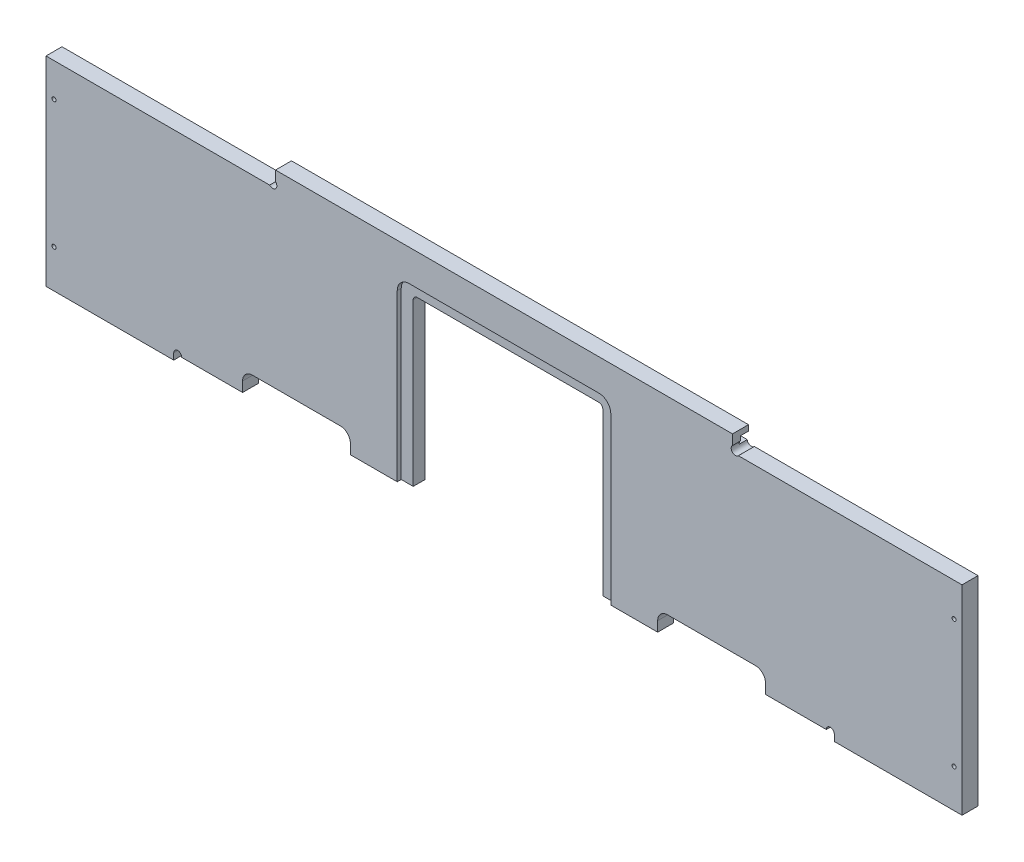
SolidWorks part; units mm, degrees
material "Pine"
ref_plane "Front Plane" through (0, 0, 0) normal (0, 0, 1) x (1, 0, 0)
ref_plane "Top Plane" through (0, 0, 0) normal (0, 1, 0) x (1, 0, 0)
ref_plane "Right Plane" through (0, 0, 0) normal (1, 0, 0) x (0, 0, -1)
sketch "Sketch1" plane through (0, 0, 0) normal (0, 0, 1) x (1, 0, 0)
  line L0 (-5300.6625, 1520.825) -> (-5451.475, 1520.825)
  line L1 (-5456.2375, 1384.3) -> (-5456.2375, 1516.0625)
  line L2 (-5557.8375, 1546.225) -> (-5194.3, 1546.225)
  line L3 (-5557.8375, 1539.875) -> (-5194.3, 1539.875)
  line L4 (-5297.4875, 1377.95) -> (-5454.65, 1377.95)
  line L5 (-5291.1375, 1384.3) -> (-5291.1375, 1516.0625)
  line L6 (-5300.6625, 1525.5875) -> (-5451.475, 1525.5875)
  line L7 (-5461, 1384.3) -> (-5461, 1516.0625)
  line L8 (-5297.4875, 1382.7125) -> (-5454.65, 1382.7125)
  line L9 (-5295.9, 1384.3) -> (-5295.9, 1516.0625)
  line L10 (-5740.4, 998.5375) -> (-5740.4, 1181.1)
  line L11 (-5740.4, 1181.1) -> (-5512.5938, 1181.1)
  line L12 (-5512.5938, 1181.1) -> (-5512.5938, 998.5375)
  line L13 (-5512.5938, 998.5375) -> (-5740.4, 998.5375)
  line L14 (-5258.5938, 1181.1) -> (-5486.4, 1181.1)
  line L15 (-5258.5938, 998.5375) -> (-5258.5938, 1181.1)
  line L16 (-5486.4, 998.5375) -> (-5258.5938, 998.5375)
  line L17 (-5486.4, 1181.1) -> (-5486.4, 998.5375)
  line L18 (-5740.4, 898.525) -> (-5011.7375, 898.525)
  line L19 (-5168.1062, 1384.3) -> (-5168.1062, 1392.2375)
  line L20 (-5176.0437, 1400.175) -> (-5245.8937, 1400.175)
  line L21 (-5253.8313, 1392.2375) -> (-5253.8313, 1384.3)
  line L22 (-5451.475, 1512.8875) -> (-5451.475, 1384.3)
  line L23 (-5303.8375, 1516.0625) -> (-5448.3, 1516.0625)
  line L24 (-5498.3062, 1384.3) -> (-5451.475, 1384.3)
  line L25 (-5253.8313, 1384.3) -> (-5300.6625, 1384.3)
  line L26 (-5584.0312, 1384.3) -> (-5740.4, 1384.3)
  line L27 (-5564.1875, 1536.7) -> (-5740.4, 1536.7)
  line L28 (-5740.4, 1357.3125) -> (-5740.4, 1206.5)
  line L29 (-5011.7375, 1357.3125) -> (-5740.4, 1357.3125)
  line L30 (-5011.7375, 1206.5) -> (-5011.7375, 1357.3125)
  line L31 (-5740.4, 1206.5) -> (-5011.7375, 1206.5)
  line L32 (-4765.675, 1549.4) -> (-4978.4, 1549.4)
  line L33 (-4765.675, 1397) -> (-4765.675, 1549.4)
  line L34 (-4978.4, 1397) -> (-4765.675, 1397)
  line L35 (-4978.4, 1549.4) -> (-4978.4, 1397)
  line L36 (-4765.675, 1371.6) -> (-4978.4, 1371.6)
  line L37 (-4765.675, 1219.2) -> (-4765.675, 1371.6)
  line L38 (-4978.4, 1219.2) -> (-4765.675, 1219.2)
  line L39 (-4978.4, 1371.6) -> (-4978.4, 1219.2)
  line L40 (-5284.7875, 803.275) -> (-5272.0875, 803.275)
  line L41 (-5187.95, 1536.7) -> (-5011.7375, 1536.7)
  line L42 (-5300.6625, 1384.3) -> (-5300.6625, 1512.8875)
  line L43 (-5740.4, 1536.7) -> (-5740.4, 1384.3)
  line L44 (-5557.8375, 1536.7) -> (-5557.8375, 1549.4)
  line L45 (-5557.8375, 1549.4) -> (-5194.3, 1549.4)
  line L46 (-5194.3, 1549.4) -> (-5194.3, 1536.7)
  line L47 (-5011.7375, 1536.7) -> (-5011.7375, 1384.3)
  line L48 (-5011.7375, 1384.3) -> (-5168.1062, 1384.3)
  line L49 (-5498.3062, 1384.3) -> (-5498.3062, 1392.2375)
  line L50 (-5506.2437, 1400.175) -> (-5576.0938, 1400.175)
  line L51 (-5584.0312, 1392.2375) -> (-5584.0312, 1384.3)
  line L52 (-5740.4, 660.4) -> (-5740.4, 898.525)
  line L53 (-5011.7375, 898.525) -> (-5011.7375, 660.4)
  line L54 (-5011.7375, 660.4) -> (-5740.4, 660.4)
  line L55 (-5291.1375, 803.275) -> (-5291.1375, 752.475)
  line L56 (-5265.7375, 752.475) -> (-5265.7375, 803.275)
  line L57 (-5284.7875, 752.475) -> (-5272.0875, 752.475)
  arc A0 (-5451.475, 1520.825) -> (-5456.2375, 1516.0625) centre (-5451.475, 1516.0625) ccw
  arc A1 (-5461, 1384.3) -> (-5454.65, 1377.95) centre (-5454.65, 1384.3) ccw
  arc A2 (-5297.4875, 1377.95) -> (-5291.1375, 1384.3) centre (-5297.4875, 1384.3) ccw
  circle A3 centre (-5037.9312, 1233.4875) radius 1.5875
  circle A4 centre (-5037.9312, 1328.7375) radius 1.5875
  circle A5 centre (-5714.2063, 1233.4875) radius 1.5875
  circle A6 centre (-5714.2063, 1328.7375) radius 1.5875
  circle A7 centre (-5018.0875, 1333.5) radius 1.5875
  circle A8 centre (-5018.0875, 1231.9) radius 1.5875
  circle A9 centre (-5734.05, 1231.9) radius 1.5875
  circle A10 centre (-5734.05, 1333.5) radius 1.5875
  circle A11 centre (-5734.05, 1511.3) radius 1.5875
  circle A12 centre (-5734.05, 1409.7) radius 1.5875
  circle A13 centre (-5018.0875, 1511.3) radius 1.5875
  circle A14 centre (-5018.0875, 1409.7) radius 1.5875
  arc A15 (-5557.8375, 1546.225) -> (-5557.8375, 1539.875) centre (-5557.8375, 1543.05) ccw
  arc A16 (-5194.3, 1539.875) -> (-5194.3, 1546.225) centre (-5194.3, 1543.05) ccw
  arc A17 (-5291.1375, 1516.0625) -> (-5300.6625, 1525.5875) centre (-5300.6625, 1516.0625) ccw
  arc A18 (-5451.475, 1525.5875) -> (-5461, 1516.0625) centre (-5451.475, 1516.0625) ccw
  arc A19 (-5456.2375, 1384.3) -> (-5454.65, 1382.7125) centre (-5454.65, 1384.3) ccw
  arc A20 (-5297.4875, 1382.7125) -> (-5295.9, 1384.3) centre (-5297.4875, 1384.3) ccw
  arc A21 (-5295.9, 1516.0625) -> (-5300.6625, 1520.825) centre (-5300.6625, 1516.0625) ccw
  circle A22 centre (-5702.3, 892.175) radius 1.5875
  circle A23 centre (-5734.05, 860.425) radius 1.5875
  circle A24 centre (-5474.8906, 892.175) radius 1.5875
  circle A25 centre (-5277.2469, 892.175) radius 1.5875
  circle A26 centre (-5049.8375, 892.175) radius 1.5875
  circle A27 centre (-5018.0875, 860.425) radius 1.5875
  circle A28 centre (-5296.6938, 1174.75) radius 1.5875
  circle A29 centre (-5448.3, 1174.75) radius 1.5875
  circle A30 centre (-5264.9437, 1155.7) radius 1.5875
  circle A31 centre (-5264.9437, 1023.9375) radius 1.5875
  circle A32 centre (-5518.9438, 1155.7) radius 1.5875
  circle A33 centre (-5518.9438, 1023.9375) radius 1.5875
  circle A34 centre (-5702.3, 1004.8875) radius 1.5875
  circle A35 centre (-5550.6937, 1004.8875) radius 1.5875
  arc A36 (-5576.0938, 1400.175) -> (-5584.0312, 1392.2375) centre (-5576.0938, 1392.2375) ccw
  arc A37 (-5168.1062, 1392.2375) -> (-5176.0437, 1400.175) centre (-5176.0437, 1392.2375) ccw
  arc A38 (-5245.8937, 1400.175) -> (-5253.8313, 1392.2375) centre (-5245.8937, 1392.2375) ccw
  arc A39 (-5448.3, 1516.0625) -> (-5451.475, 1512.8875) centre (-5448.3, 1512.8875) ccw
  arc A40 (-5284.7875, 803.275) -> (-5291.1375, 803.275) centre (-5287.9625, 803.275) ccw
  circle A41 centre (-5679.2812, 1026.3187) radius 1.5875
  circle A42 centre (-5679.2812, 1153.3187) radius 1.5875
  circle A43 centre (-5571.3313, 1153.3187) radius 1.5875
  circle A44 centre (-5571.3313, 1026.3187) radius 1.5875
  circle A45 centre (-5317.3312, 1153.3187) radius 1.5875
  circle A46 centre (-5317.3312, 1026.3187) radius 1.5875
  circle A47 centre (-5425.2812, 1026.3187) radius 1.5875
  circle A48 centre (-5425.2812, 1153.3187) radius 1.5875
  arc A49 (-5194.3, 1536.7) -> (-5187.95, 1536.7) centre (-5191.125, 1536.7) ccw
  arc A50 (-5564.1875, 1536.7) -> (-5557.8375, 1536.7) centre (-5561.0125, 1536.7) ccw
  arc A51 (-5300.6625, 1512.8875) -> (-5303.8375, 1516.0625) centre (-5303.8375, 1512.8875) ccw
  arc A52 (-5498.3062, 1392.2375) -> (-5506.2437, 1400.175) centre (-5506.2437, 1392.2375) ccw
  circle A53 centre (-5712.46, 784.225) radius 4.7625
  arc A54 (-5272.0875, 752.475) -> (-5265.7375, 752.475) centre (-5268.9125, 752.475) ccw
  arc A55 (-5291.1375, 752.475) -> (-5284.7875, 752.475) centre (-5287.9625, 752.475) ccw
  circle A56 centre (-5182.3938, 684.2125) radius 3.175
  circle A57 centre (-5239.5437, 684.2125) radius 3.175
  circle A58 centre (-5512.5938, 684.2125) radius 3.175
  circle A59 centre (-5569.7437, 684.2125) radius 3.175
  circle A60 centre (-5474.8906, 666.75) radius 1.5875
  circle A61 centre (-5277.2469, 666.75) radius 1.5875
  circle A62 centre (-5734.05, 698.5) radius 1.5875
  circle A63 centre (-5702.3, 666.75) radius 1.5875
  circle A64 centre (-5049.8375, 666.75) radius 1.5875
  circle A65 centre (-5018.0875, 698.5) radius 1.5875
  circle A66 centre (-5713.73, 835.025) radius 4.7625
  circle A67 centre (-5712.46, 819.785) radius 4.7625
  circle A68 centre (-5712.46, 802.005) radius 4.7625
  circle A69 centre (-5714.2063, 1314.45) radius 3.175
  circle A70 centre (-5037.9312, 1314.45) radius 3.175
  arc A71 (-5265.7375, 803.275) -> (-5272.0875, 803.275) centre (-5268.9125, 803.275) ccw
  ellipse E0 centre (-5371.3062, 1089.8188) end of major axis (-5277.6438, 1089.8188) minor radius 65.0875
  ellipse E1 centre (-5625.3062, 1089.8188) end of major axis (-5531.6438, 1089.8188) minor radius 65.0875
sketch "Sketch2" plane through (0, 0, 0) normal (0, 0, 1) x (1, 0, 0)
  line L0 (-5740.4, 1537.97) -> (-5740.4, 1384.3)
  line L1 (-5740.4, 1384.3) -> (-5584.0312, 1384.3)
  line L2 (-5584.0312, 1384.3) -> (-5584.0312, 1392.2375)
  line L3 (-5576.0938, 1400.175) -> (-5506.2437, 1400.175)
  line L4 (-5498.3062, 1392.2375) -> (-5498.3062, 1384.3)
  line L5 (-5498.3062, 1384.3) -> (-5451.475, 1384.3)
  line L6 (-5451.475, 1384.3) -> (-5451.475, 1512.8875)
  line L7 (-5448.3, 1516.0625) -> (-5303.8375, 1516.0625)
  line L8 (-5300.6625, 1512.8875) -> (-5300.6625, 1384.3)
  line L9 (-5300.6625, 1384.3) -> (-5253.8313, 1384.3)
  line L10 (-5253.8313, 1384.3) -> (-5253.8313, 1392.2375)
  line L11 (-5245.8937, 1400.175) -> (-5176.0437, 1400.175)
  line L12 (-5168.1062, 1392.2375) -> (-5168.1062, 1384.3)
  line L13 (-5168.1062, 1384.3) -> (-5011.7375, 1384.3)
  line L14 (-5011.7375, 1384.3) -> (-5011.7375, 1537.97)
  line L15 (-5011.7375, 1537.97) -> (-5194.3, 1537.97)
  line L16 (-5194.3, 1537.97) -> (-5194.3, 1550.67)
  line L17 (-5194.3, 1550.67) -> (-5557.8375, 1550.67)
  line L18 (-5557.8375, 1550.67) -> (-5557.8375, 1537.97)
  line L19 (-5557.8375, 1537.97) -> (-5740.4, 1537.97)
  arc A0 (-5584.0312, 1392.2375) -> (-5576.0938, 1400.175) centre (-5576.0938, 1392.2375) cw
  arc A1 (-5506.2437, 1400.175) -> (-5498.3062, 1392.2375) centre (-5506.2437, 1392.2375) cw
  arc A2 (-5451.475, 1512.8875) -> (-5448.3, 1516.0625) centre (-5448.3, 1512.8875) cw
  arc A3 (-5303.8375, 1516.0625) -> (-5300.6625, 1512.8875) centre (-5303.8375, 1512.8875) cw
  arc A4 (-5253.8313, 1392.2375) -> (-5245.8937, 1400.175) centre (-5245.8938, 1392.2375) cw
  arc A5 (-5176.0437, 1400.175) -> (-5168.1062, 1392.2375) centre (-5176.0437, 1392.2375) cw
  dimension "D1" = 12.7
  dimension "D2" = 166.37
extrude "Extrude1" add sketch "Sketch2" against normal blind 12.7
sketch "Sketch6" plane through (0, 0, 0) normal (0, 0, 1) x (1, 0, 0)
  line L0 (-5557.8375, 1537.97) -> (-5560.0826, 1540.2151) construction
  line L1 (-5194.3, 1537.97) -> (-5192.0549, 1540.2151) construction
  line L2 (-5557.8375, 1537.97) -> (-5740.4, 1537.97) construction
  line L3 (-5011.7375, 1537.97) -> (-5194.3, 1537.97) construction
  circle A0 centre (-5560.0826, 1540.2151) radius 3.302
  circle A1 centre (-5192.0549, 1540.2151) radius 3.302
  dimension "D1" = 45
  dimension "D2" = 3.175
  dimension "D3" = 45
  dimension "D4" = 3.175
extrude "Cut-Extrude4" cut sketch "Sketch6" against normal up to surface (12.7 mm away) up to face at (-5376.0688, 1444.7331, -12.7)
sketch "Sketch3" plane through (0, 0, 0) normal (0, 0, 1) x (1, 0, 0)
  line L0 (-5297.4875, 1377.95) -> (-5454.65, 1377.95)
  line L1 (-5461, 1384.3) -> (-5461, 1516.0625)
  line L2 (-5451.475, 1525.5875) -> (-5300.6625, 1525.5875)
  line L3 (-5291.1375, 1516.0625) -> (-5291.1375, 1384.3)
  arc A0 (-5454.65, 1377.95) -> (-5461, 1384.3) centre (-5454.65, 1384.3) cw
  arc A1 (-5461, 1516.0625) -> (-5451.475, 1525.5875) centre (-5451.475, 1516.0625) cw
  arc A2 (-5300.6625, 1525.5875) -> (-5291.1375, 1516.0625) centre (-5300.6625, 1516.0625) cw
  arc A3 (-5291.1375, 1384.3) -> (-5297.4875, 1377.95) centre (-5297.4875, 1384.3) cw
extrude "Cut-Extrude1" cut sketch "Sketch3" against normal blind 3.175
sketch "Sketch4" plane through (0, 0, 0) normal (0, 0, 1) x (1, 0, 0)
  circle A0 centre (-5734.05, 1511.3) radius 1.5875
  circle A1 centre (-5734.05, 1409.7) radius 1.5875
  circle A2 centre (-5018.0875, 1409.7) radius 1.5875
  circle A3 centre (-5018.0875, 1511.3) radius 1.5875
extrude "Cut-Extrude2" cut sketch "Sketch4" against normal up to surface (12.7 mm away) up to face at (-5376.0688, 1451.5531, -12.7)
sketch "Sketch5" plane through (0, 0, -12.7) normal (0, 0, -1) x (-1, 0, 0)
  line L0 (5557.8375, 1539.875) -> (5557.8375, 1546.225)
  line L1 (5557.8375, 1546.225) -> (5194.3, 1546.225)
  line L2 (5194.3, 1546.225) -> (5194.3, 1539.875)
  line L3 (5194.3, 1539.875) -> (5557.8375, 1539.875)
extrude "Cut-Extrude3" cut sketch "Sketch5" against normal blind 6.35
sketch "Sketch7" plane through (0, 0, 0) normal (0, 0, 1) x (1, 0, 0)
  line L0 (-5740.4, 1384.3) -> (-5740.4, 1379.22)
  line L1 (-5740.4, 1379.22) -> (-5638.8, 1379.22)
  line L2 (-5740.4, 1384.3) -> (-5584.0312, 1384.3) construction
  line L3 (-5638.8, 1384.3) -> (-5740.4, 1384.3)
  line L4 (-5638.8, 1379.22) -> (-5638.8, 1384.3)
  line L5 (-5011.7375, 1384.3) -> (-5011.7375, 1379.22)
  line L6 (-5011.7375, 1379.22) -> (-5113.3375, 1379.22)
  line L7 (-5113.3375, 1384.3) -> (-5011.7375, 1384.3)
  line L8 (-5168.1062, 1384.3) -> (-5011.7375, 1384.3) construction
  line L9 (-5113.3375, 1384.3) -> (-5113.3375, 1379.22)
  dimension "D1" = 5.08
  dimension "D2" = 101.6
  dimension "D3" = 101.6
extrude "Extrude2" add sketch "Sketch7" against normal up to surface (12.7 mm away) up to face at (-5376.0688, 1443.7612, -12.7)
sketch "Sketch8" plane through (0, 0, 0) normal (0, 0, 1) x (1, 0, 0)
  line L0 (-5638.8, 1384.3) -> (-5632.45, 1384.3) construction
  line L1 (-5638.8, 1384.3) -> (-5584.0312, 1384.3) construction
  line L2 (-5113.3375, 1384.3) -> (-5119.6875, 1384.3) construction
  line L3 (-5168.1062, 1384.3) -> (-5113.3375, 1384.3) construction
  circle A0 centre (-5635.625, 1384.3) radius 3.175
  circle A1 centre (-5116.5125, 1384.3) radius 3.175
extrude "Cut-Extrude5" cut sketch "Sketch8" against normal up to surface (12.7 mm away) up to face at (-5376.0688, 1435.1557, -12.7)
